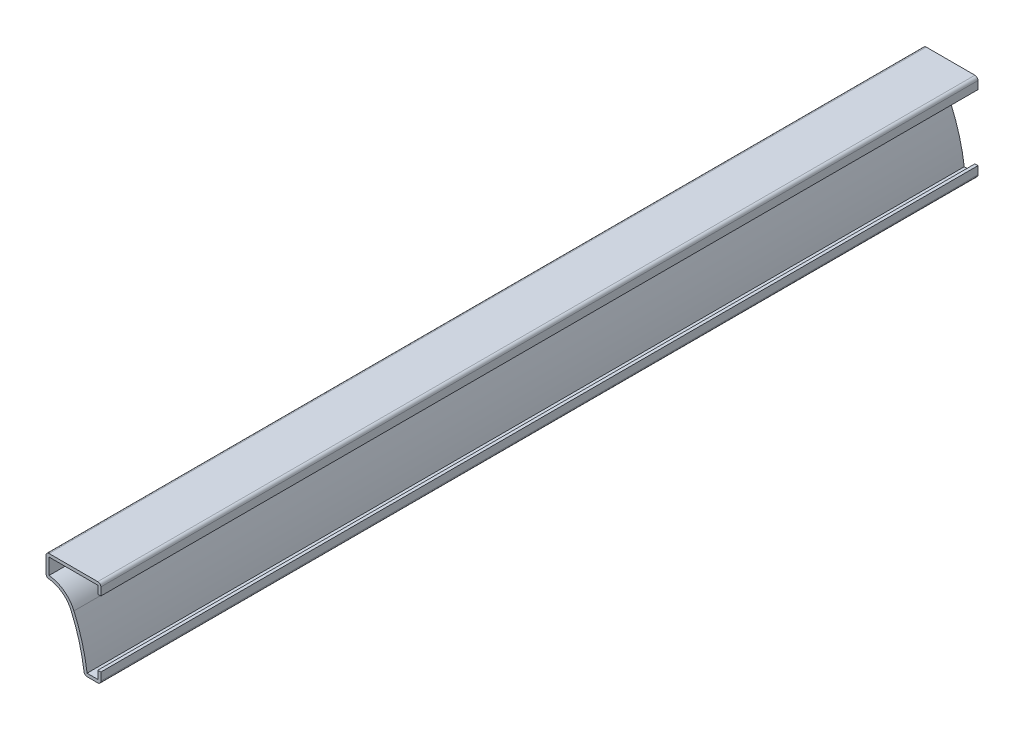
SolidWorks part; units mm, degrees
ref_plane "Front Plane" through (0, 0, 0) normal (0, 0, 1) x (1, 0, 0)
ref_plane "Top Plane" through (0, 0, 0) normal (0, 1, 0) x (1, 0, 0)
ref_plane "Right Plane" through (0, 0, 0) normal (1, 0, 0) x (0, 0, -1)
sketch "Sketch1" plane through (0, 0, 0) normal (0, 0, 1) x (1, 0, 0)
  line L0 (0, 3.175) -> (0, 0)
  line L1 (0, 0) -> (-4.7625, 0)
  line L2 (-15.875, 19.05) -> (-15.875, 25.4)
  line L3 (-15.875, 25.4) -> (0, 25.4)
  line L4 (0, 25.4) -> (0, 22.225)
  arc A0 (-4.7625, 0) -> (-8.589, 14.2618) centre (-55.2195, -5.8936) ccw
  arc A1 (-8.589, 14.2618) -> (-15.875, 19.05) centre (-15.875, 11.1125) ccw
  point P8 (0, 0)
  point P12 (-9.0058, 14.573)
  point P13 (-6.4127, 11.648)
  point P14 (-6.7403, 11.3889)
  point P15 (-9.3905, 15.0155)
  point P16 (-10.3269, 15.7889)
  point P17 (-10.3269, 15.7889)
  dimension "D7" = 7.9375
  dimension "D8" = 50.8
  dimension "D1" = 25.4
  dimension "D2" = 15.875
  dimension "D3" = 3.175
  dimension "D4" = 3.175
  dimension "D5" = 4.7625
  dimension "D6" = 6.35
extrude "Extrude-Thin1" add sketch "Sketch1" against normal blind 254 thin
fillet "Fillet1" radius 0.889 5 edges at (-4.7625, 0, -127) (0, 0, -127) (-15.875, 19.05, -127) (-15.875, 25.4, -127) (0, 25.4, -127)
